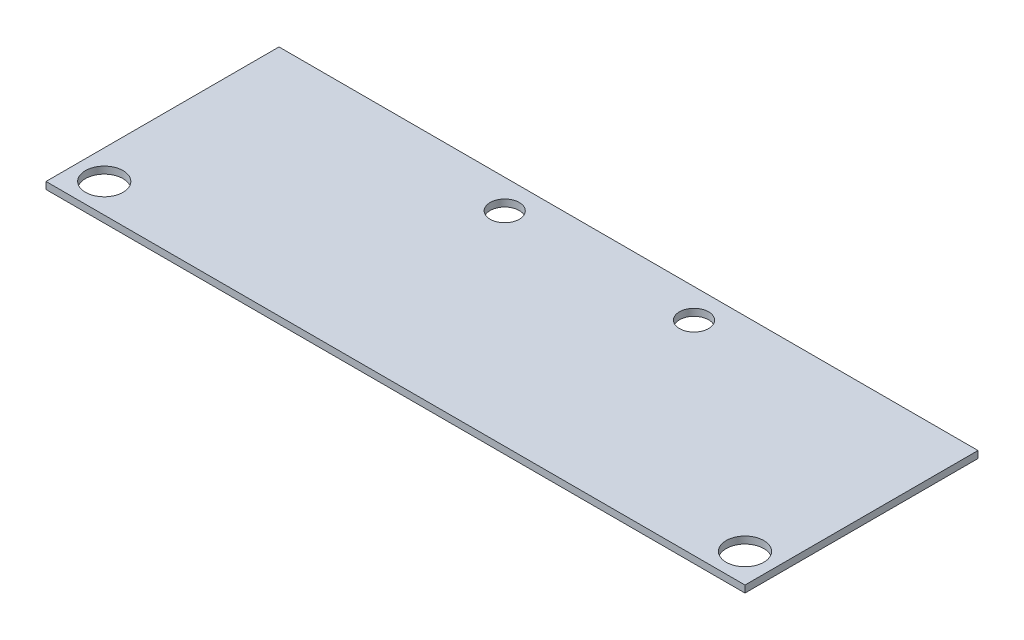
SolidWorks part; units mm, degrees
ref_plane "Front Plane" through (0, 0, 0) normal (0, 0, 1) x (1, 0, 0)
ref_plane "Top Plane" through (0, 0, 0) normal (0, 1, 0) x (1, 0, 0)
ref_plane "Right Plane" through (0, 0, 0) normal (1, 0, 0) x (0, 0, -1)
sketch "Sketch1" plane through (0, 0, 0) normal (0, 1, 0) x (1, 0, 0)
  line L0 (-50.2216, -45.1077) -> (102.1784, -45.1077)
  line L1 (102.1784, -45.1077) -> (102.1784, 5.6923)
  line L2 (102.1784, 5.6923) -> (51.3784, 5.6923)
  line L3 (51.3784, 5.6923) -> (0.5784, 5.6923)
  line L4 (0.5784, 5.6923) -> (-50.2216, 5.6923)
  line L5 (-50.2216, 5.6923) -> (-50.2216, -45.1077)
  point P2 (0, 0)
  point P7 (0, 0)
  dimension "D1" = 50.8
  dimension "D2" = 152.4
  dimension "D3" = 50.8
  dimension "D4" = 50.8
  dimension "D5" = 50.8
  dimension "D7" = 50.8
extrude "Boss-Extrude1" add sketch "Sketch1" along normal blind 1.524
sketch "Sketch2" plane through (0, 1.524, 0) normal (0, 1, 0) x (1, 0, 0)
  line L0 (-50.2216, 5.6923) -> (-50.2216, -45.1077) construction
  line L1 (102.1784, 5.6923) -> (-50.2216, 5.6923) construction
  line L2 (-50.2216, -45.1077) -> (102.1784, -45.1077) construction
  line L3 (-50.2216, 5.6923) -> (-50.2216, -45.1077) construction
  circle A0 centre (-43.8716, -38.7577) radius 4.1021
  circle A1 centre (95.8284, -38.7577) radius 4.1021
  circle A2 centre (46.6159, -0.6577) radius 3.175
  circle A3 centre (5.3409, -0.6577) radius 3.175
  dimension "D3" = 8.2042
  dimension "D4" = 8.2042
  dimension "D7" = 6.35
  dimension "D8" = 6.35
  dimension "D9" = 6.35
  dimension "D1" = 139.7
  dimension "D2" = 44.45
  dimension "D5" = 6.35
  dimension "D6" = 41.275
  dimension "D10" = 6.35
  dimension "D11" = 6.35
  dimension "D12" = 44.45
  dimension "D13" = 6.35
  dimension "D14" = 6.35
  dimension "D15" = 55.5625
extrude "Cut-Extrude1" cut sketch "Sketch2" against normal through all
